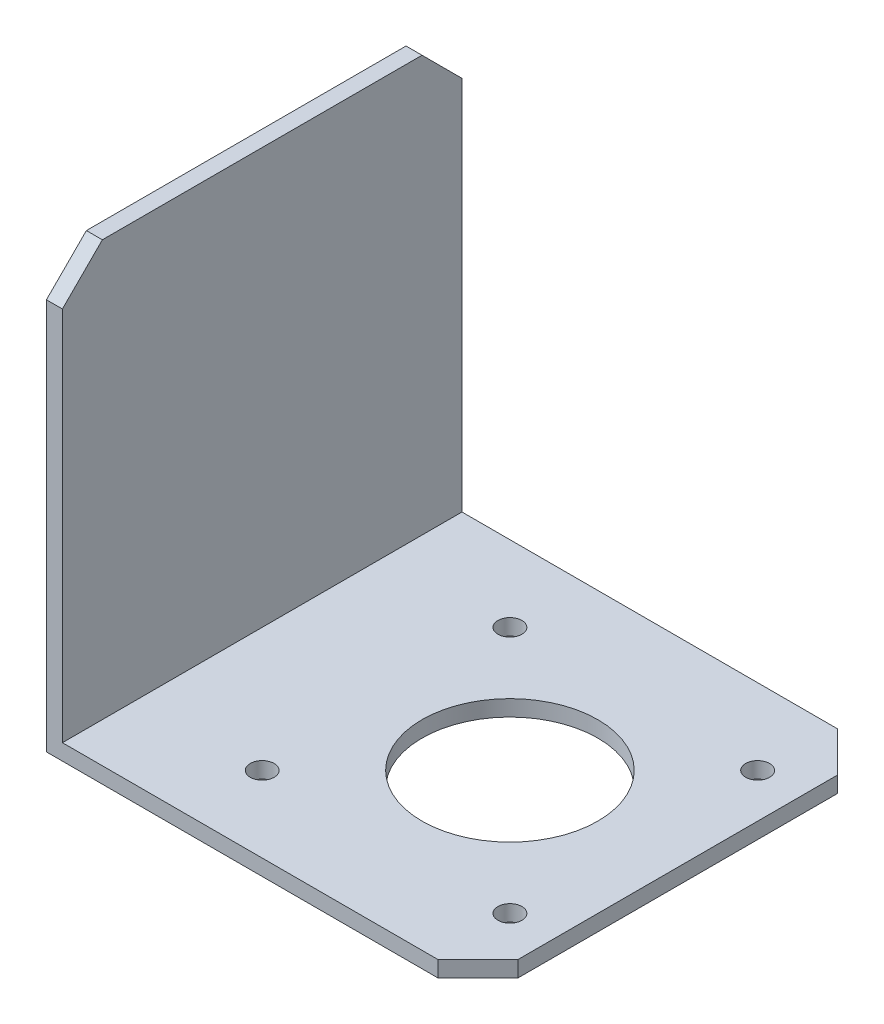
SolidWorks part; units mm, degrees
ref_plane "Front Plane" through (0, 0, 0) normal (0, 0, 1) x (1, 0, 0)
ref_plane "Top Plane" through (0, 0, 0) normal (0, 1, 0) x (1, 0, 0)
ref_plane "Right Plane" through (0, 0, 0) normal (1, 0, 0) x (0, 0, -1)
sketch "Sketch1" plane through (0, 0, 0) normal (0, 0, 1) x (1, 0, 0)
  line L0 (0, 0) -> (0, 52)
  line L1 (0, 0) -> (52, 0)
  dimension "D1" = 52
  dimension "D2" = 52
extrude "Extrude-Thin1" add sketch "Sketch1" along normal blind 50 thin thin type one direction wall 2
chamfer "Chamfer1" distance 5 angle 45 4 edges at (-1, 52, 0) (52, -1, 0) (52, -1, 50) (-1, 52, 50)
sketch "Sketch2" plane through (0, -2, 0) normal (0, -1, 0) x (1, 0, 0)
  line L0 (52, 45) -> (52, 5) construction
  line L1 (10, 46) -> (52, 46)
  line L2 (10, 46) -> (10, 4)
  line L3 (10, 4) -> (52, 4)
  line L4 (52, 46) -> (52, 4)
  line L5 (10, 46) -> (52, 4) construction
  line L6 (10, 4) -> (52, 46) construction
  line L7 (-2, 50) -> (-2, 0) construction
  line L9 (15.5, 40.5) -> (46.5, 40.5)
  line L10 (15.5, 40.5) -> (15.5, 9.5)
  line L11 (15.5, 9.5) -> (46.5, 9.5)
  line L12 (46.5, 40.5) -> (46.5, 9.5)
  line L13 (15.5, 40.5) -> (46.5, 9.5) construction
  line L14 (15.5, 9.5) -> (46.5, 40.5) construction
  circle A0 centre (31, 25) radius 11
  circle A1 centre (15.5, 40.5) radius 1.5
  circle A2 centre (46.5, 40.5) radius 1.5
  circle A3 centre (46.5, 9.5) radius 1.5
  circle A4 centre (15.5, 9.5) radius 1.5
  point P0 (31, 25)
  point P7 (10, 25)
  point P10 (-2, 25)
  dimension "D3" = 22
  dimension "D6" = 3
  dimension "D1" = 42
  dimension "D2" = 42
  dimension "D4" = 31
  dimension "D5" = 31
extrude "Cut-Extrude1" cut sketch "Sketch2" against normal blind 10 contours A2 | A3 | A4 | A1 | A0
